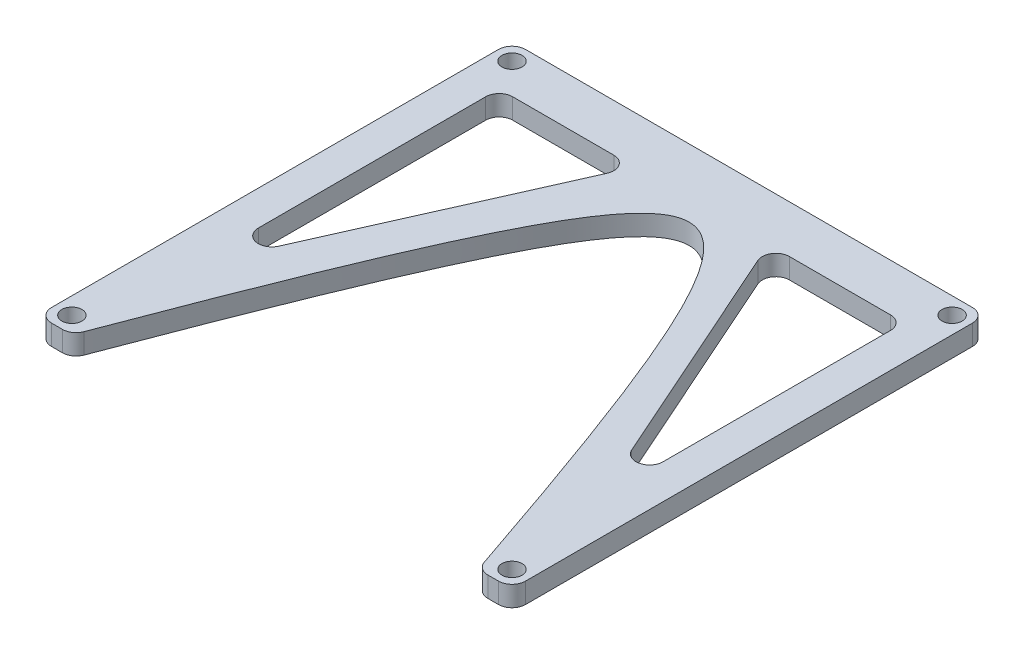
SolidWorks part; units mm, degrees
ref_plane "Front Plane" through (0, 0, 0) normal (0, 0, 1) x (1, 0, 0)
ref_plane "Top Plane" through (0, 0, 0) normal (0, 1, 0) x (1, 0, 0)
ref_plane "Right Plane" through (0, 0, 0) normal (1, 0, 0) x (0, 0, -1)
sketch "Sketch2" plane through (0, 0, 0) normal (0, 1, 0) x (1, 0, 0)
  line L0 (-30, -35) -> (-35, -35)
  line L1 (-35, 35) -> (35, 35)
  line L2 (-35, 35) -> (-35, -35)
  line L3 (-35, -35) -> (35, -35) construction
  line L4 (35, 35) -> (35, -35)
  line L5 (-35, 35) -> (35, -35) construction
  line L6 (-35, -35) -> (35, 35) construction
  line L7 (35, -35) -> (30, -35)
  conic Q0 (-30, -35) -> (30, -35) control (1.6055, 49.1023) rho 0.713417
  point P0 (0, 0)
  point P6 (0, 0)
  dimension "D3" = 60
  dimension "D1" = 70
  dimension "D2" = 70
  dimension "D4" = 5
  dimension "D5" = 60
extrude "Boss-Extrude1" add sketch "Sketch2" along normal blind 3
sketch "Sketch3" plane through (0, 3, 0) normal (0, 1, 0) x (1, 0, 0)
  line L0 (-35, 35) -> (-35, -35) construction
  line L1 (35, 35) -> (-35, 35) construction
  circle A0 centre (-32.5, 32.5) radius 1.4881
  circle A1 centre (32.5, 32.5) radius 1.4881
  circle A2 centre (32.5, -32.5) radius 1.4881
  circle A3 centre (-32.5, -32.5) radius 1.4881
  dimension "D1" = 2.9763
  dimension "D2" = 2.5
  dimension "D3" = 2.5
  dimension "D4" = 2
extrude "Cut-Extrude1" cut sketch "Sketch3" against normal through all
fillet "Fillet1" radius 2 6 edges at (35, 1.5, 35) (30, 1.5, 35) (-30, 1.5, 35) (-35, 1.5, 35) (-35, 1.5, -35) (35, 1.5, -35)
sketch "Sketch4" plane through (0, 3, 0) normal (0, 1, 0) x (1, 0, 0)
  line L0 (-29.8916, -17) -> (-29.8916, 28)
  line L1 (-29.8916, 28) -> (-9.8916, 28)
  line L2 (-9.8916, 28) -> (-29.8916, -17)
  line L3 (0, 49.3751) -> (0, -57.6391) construction
  line L4 (29.8916, -17) -> (29.8916, 28)
  line L5 (29.8916, 28) -> (9.8916, 28)
  line L6 (9.8916, 28) -> (29.8916, -17)
  line L7 (33, 35) -> (-33, 35) construction
  dimension "D1" = 45
  dimension "D2" = 20
  dimension "D3" = 7
extrude "Cut-Extrude2" cut sketch "Sketch4" against normal through all
fillet "Fillet2" radius 2 6 edges at (29.8916, 1.5, -28) (9.8916, 1.5, -28) (29.8916, 1.5, 17) (-29.8916, 1.5, 17) (-29.8916, 1.5, -28) (-9.8916, 1.5, -28)
